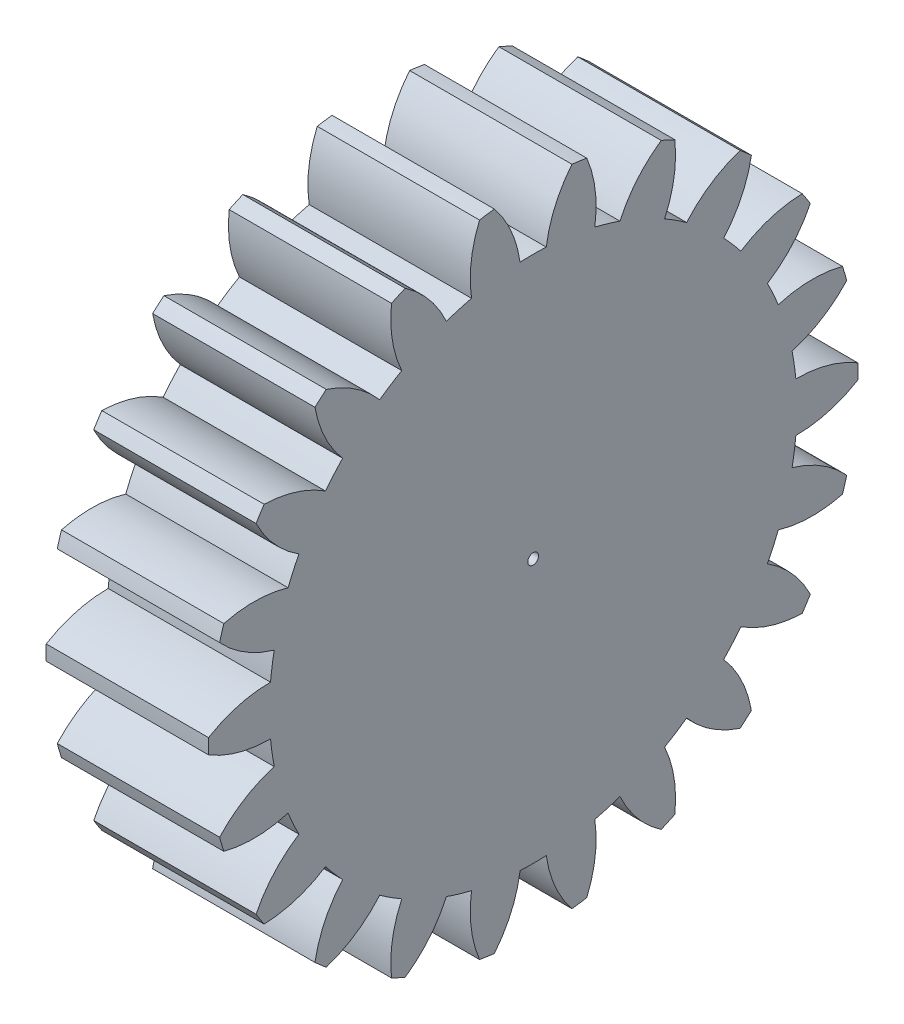
SolidWorks part; units mm, degrees
ref_plane "Plane1" through (0, 0, 0) normal (0, 0, 1) x (1, 0, 0)
ref_plane "Plane2" through (0, 0, 0) normal (0, 1, 0) x (1, 0, 0)
ref_plane "Plane3" through (0, 0, 0) normal (1, 0, 0) x (0, 0, -1)
sketch "HoldingSke" plane through (0, 0, 0) normal (0, 1, 0) x (1, 0, 0)
  line L0 (0, 0) -> (0.4636, -0.1873)
  line L1 (-15, 0) -> (100, 0) construction
  line L2 (0, 0) -> (-2.1039, 2.3779)
  line L3 (0, 0) -> (-11.863, 4.5341)
  line L4 (0, 0) -> (8.0072, 3.2351)
  line L5 (0, 0) -> (-46.8476, -17.4728)
  line L6 (0, 0) -> (-9.9476, -6.7116)
  line L7 (-2.1039, 2.3779) -> (8.6586, 51.2059)
  line L8 (-76.2, 54.61) -> (-76.1, 54.61)
  line L9 (-71.009, 38.7566) -> (-53.1078, 45.2721)
  line L10 (-76.2, 71.12) -> (104.1128, 71.12)
  line L11 (0, 0) -> (-12, 0)
  line L12 (-76.2, 101.6) -> (-76.133, 101.6)
  line L13 (24.9733, 27.94) -> (52.9518, 28.4284)
  line L14 (24.9733, 27.94) -> (24.9743, 27.94)
  line L15 (24.9733, 27.94) -> (100.4006, 29.5858)
  line L16 (-63.627, -2) -> (-12.827, -2)
  circle A0 centre (0, 0) radius 0.4
  circle A1 centre (0, 0) radius 19.499
  circle A2 centre (0, 0) radius 37.5
  circle A3 centre (0, 0) radius 0.4
  dimension "Hub_dia" = 75
  dimension "Bore" = 0.8
  dimension "MBD" = 0.8
  dimension "Overall_len" = 50
  dimension "Thickness" = 12
  dimension "OAL" = 50.0001
  dimension "T_dim" = 0.1
  dimension "Ap" = 20
  dimension "H" = 19.05
  dimension "Pitch_radius" = 180.3128
  dimension "Width" = 12
  dimension "Addendum_fac" = 1
  dimension "Dedendum_fac" = 1.25
  dimension "Clearance_fac" = 0.25
  dimension "Dedendum_add" = 0.001
sketch "BasProSke" plane through (0, 0, 0) normal (0, 1, 0) x (1, 0, 0)
  line L0 (-10, 0) -> (60, 0) construction
  line L1 (0, 0) -> (0, 24)
  line L2 (0, 0) -> (12, 0)
  line L3 (12, 0) -> (12, 24)
  line L4 (12, 24) -> (0, 24)
  dimension "Thickness" = 12
revolve "Base-Revolve" add sketch "BasProSke" angle 360 about L0
sketch "TooCutSke" plane through (0, 0, 0) normal (1, 0, 0) x (0, 0, -1)
  line L1 (0, 0) -> (0, 107) construction
  line L2 (0, 0) -> (-1.6867, 21.9352) construction
  line L3 (0, 0) -> (-6.2482, 43.4572) construction
  line L4 (-1.6867, 21.9352) -> (-3.1241, 21.7286) construction
  arc A0 (0.9682, 19.4749) -> (-0.9682, 19.4749) centre (0, 0) ccw
  arc A1 (2.8856, 23.8515) -> (-2.8856, 23.8515) centre (0, 0) ccw
  circle A2 centre (0, 0) radius 22 construction
  circle A3 centre (0, 0) radius 20.6732 construction
  arc A4 (-0.9682, 19.4749) -> (-2.8856, 23.8515) centre (-9.6845, 18.2645) ccw
  arc A5 (2.8856, 23.8515) -> (0.9682, 19.4749) centre (9.6845, 18.2645) ccw
extrude "ToothCut" cut sketch "TooCutSke" along normal through all
fillet "Breaks" [suppressed] radius 0.04
fillet "RootFillets" [suppressed] radius 0.501
pattern_circular "TeethCuts" count 22 every 16.364 about axis through (-10, 0, 0) along (1, 0, 0) of "ToothCut", "RootFillets", "Breaks"
sketch "HubNeaOneSke" plane through (0, 0, 0) normal (-1, 0, 0) x (0, 0, 1)
  circle A0 centre (0, 0) radius 19.499
extrude "HubNearOne" [suppressed] add sketch "HubNeaOneSke" along normal blind 38.0001
sketch "HubNeaBotSke" plane through (0, 0, 0) normal (-1, 0, 0) x (0, 0, 1)
  circle A0 centre (0, 0) radius 19.499
extrude "HubNearBoth" [suppressed] add sketch "HubNeaBotSke" along normal blind 19
ref_plane "FarPln" through (12, 0, 0) normal (1, 0, 0) x (0, 0, -1)
sketch "HubFarSke" plane through (12, 0, 0) normal (1, 0, 0) x (0, 0, -1)
  circle A0 centre (0, 0) radius 19.499
extrude "HubFar" [suppressed] add sketch "HubFarSke" along normal blind 19
sketch "BorSke" plane through (0, 0, 0) normal (1, 0, 0) x (0, 0, -1)
  circle A0 centre (0, 0) radius 0.4
  dimension "Diameter" = 0.8
extrude "Bore" cut sketch "BorSke" along normal mid plane 100.0001
sketch "KeySke" plane through (0, 0, 0) normal (1, 0, 0) x (0, 0, -1)
  line L0 (-0.05, 0) -> (-0.05, 0.5)
  line L1 (-0.05, 0.5) -> (0.05, 0.5)
  line L2 (0.05, 0.5) -> (0.05, 0)
  line L3 (0, 0) -> (0, 34) construction
  line L4 (-0.05, 0) -> (0.05, 0)
  dimension "Offset" = 0.5
  dimension "Width" = 0.1
extrude "Keyway" [suppressed] cut sketch "KeySke" along normal mid plane 100.0001
pattern_circular "Keyway2" [suppressed] count 2 every 90 about axis through (-10, 0, 0) along (1, 0, 0)
equation "' \"Module@HoldingSke\" = 6.35"
equation "' \"Num_teeth@HoldingSke\" = 12"
equation "' \"Ap@HoldingSke\" =  20"
equation "' \"Ap@HoldingSke\" = 20"
equation "' \"Width@HoldingSke\" = 0.5 * 25.4"
equation "' \"Hub_dia@HoldingSke\"= 1 * 25.4"
equation "' \"Hub_dia@HoldingSke\" = 1 * 25.4"
equation "' \"Overall_len@HoldingSke\" = 1.0 * 25.4"
equation "' \"Bore@HoldingSke\" = 0.75 * 25.4"
equation "' \"T_dim@HoldingSke\" = 0.1 * 25.4"
equation "' \"Width@KeySke\" = 0.25 * 25.4"
equation "' \"Show_teeth@HoldingSke\" = 13"
equation "' \"Backlash@HoldingSke\" = 0.009 * 25.4"
equation "' \"Addendum_fac@HoldingSke\" = 1.0"
equation "' \"Dedendum_fac@HoldingSke\" = 1.25"
equation "' \"Dedendum_add@HoldingSke\" = 0.00005 * 25.4"
equation "' \"Clearance_fac@HoldingSke\" = 0.25"
equation "\"Pitch@HoldingSke\" = 1 / \"Module@HoldingSke\""
equation "\"Overcut_dia@TooCutSke\" = (\"Num_teeth@HoldingSke\" + 2 * \"Addendum_fac@HoldingSke\") / \"Pitch@HoldingSke\" + 0.002 * 25.4"
equation "\"Pitch_dia@TooCutSke\" = \"Num_teeth@HoldingSke\" / \"Pitch@HoldingSke\""
equation "\"Base_dia@TooCutSke\" = \"Num_teeth@HoldingSke\" / \"Pitch@HoldingSke\" * cos((\"Ap@HoldingSke\"  * 3.14159265 / 180))"
equation "\"Root_dia@TooCutSke\" = (\"Num_teeth@HoldingSke\" + 2) / \"Pitch@HoldingSke\" - 2 * (\"Addendum_fac@HoldingSke\" + \"Dedendum_fac@HoldingSke\") / \"Pitch@HoldingSke\" - \"Dedendum_add@HoldingSke\" * 2"
equation "\"Half_ang@TooCutSke\" = 180 / \"Num_teeth@HoldingSke\""
equation "\"Half_CT@TooCutSke\" = \"Num_teeth@HoldingSke\" / \"Pitch@HoldingSke\" * sin((3.14159265 / 2 / \"Num_teeth@HoldingSke\")) / 2 - 7 * \"Backlash@HoldingSke\" / 4"
equation "\"Flank_rad@TooCutSke\" = \"Num_teeth@HoldingSke\" / \"Pitch@HoldingSke\" / 5"
equation "\"Radius@RootFillets\" = \"Clearance_fac@HoldingSke\" / \"Pitch@HoldingSke\" + \"Dedendum_add@HoldingSke\""
equation "\"Break_rad@Breaks\" = 0.02 / \"Pitch@HoldingSke\""
equation "\"Thickness@HoldingSke\" = \"Width@HoldingSke\""
equation "\"OAL@HoldingSke\" = \"Thickness@HoldingSke\""
equation "\"MHD@HoldingSke\" = (\"Num_teeth@HoldingSke\" + 2) / \"Pitch@HoldingSke\" - 2 * (\"Addendum_fac@HoldingSke\" + \"Dedendum_fac@HoldingSke\")  / \"Pitch@HoldingSke\" - \"Dedendum_add@HoldingSke\" * 2"
equation "\"MBD@HoldingSke\" = (\"Num_teeth@HoldingSke\" + 2) / \"Pitch@HoldingSke\" - 2 * (\"Addendum_fac@HoldingSke\" + \"Dedendum_fac@HoldingSke\")  / \"Pitch@HoldingSke\" - \"Dedendum_add@HoldingSke\" * 2 - 0.002 * 25.4"
equation "\"MHD@HoldingSke\" = ((sgn( \"MHD@HoldingSke\" - \"Hub_dia@HoldingSke\" )-1)*( \"MHD@HoldingSke\" - \"Hub_dia@HoldingSke\" ))/-2+ \"Hub_dia@HoldingSke\""
equation "\"MBD@HoldingSke\" = ((sgn( \"MBD@HoldingSke\" - \"Bore@HoldingSke\" )-1)*( \"MBD@HoldingSke\" - \"Bore@HoldingSke\" ))/-2+ \"Bore@HoldingSke\""
equation "\"OAL@HoldingSke\" = ((sgn( \"OAL@HoldingSke\" - \"Overall_len@HoldingSke\" )+1)*( \"OAL@HoldingSke\" - \"Overall_len@HoldingSke\" ))/2 + \"Overall_len@HoldingSke\" + 0.000002 * 25.4"
equation "\"Num_teeth@TeethCuts\" = int( \"Show_teeth@HoldingSke\" ) + 1"
equation "\"Num_teeth@TeethCuts\" = ((sgn( \"Num_teeth@TeethCuts\" - \"Num_teeth@HoldingSke\" )-1)*( \"Num_teeth@TeethCuts\" - \"Num_teeth@HoldingSke\" ))/-2+ \"Num_teeth@HoldingSke\""
equation "\"Num_teeth@TeethCuts\" = ((sgn( \"Num_teeth@TeethCuts\" - 2.0)+1)*( \"Num_teeth@TeethCuts\" - 2.0))/2 +2.0"
equation "\"Angle@TeethCuts\" = 360.0 / \"Num_teeth@HoldingSke\""
equation "\"Diameter@BasProSke\" = (\"Num_teeth@HoldingSke\" + 2 * \"Addendum_fac@HoldingSke\") / \"Pitch@HoldingSke\""
equation "\"Thickness@BasProSke\"  = \"Thickness@HoldingSke\""
equation "' \"Fillet_rad@BasProSke\" =  \"Thickness@HoldingSke\" * 0.05"
equation "' \"Fillet_rad@BasProSke\" = \"Thickness@HoldingSke\" * 0.05"
equation "\"MHD@HoldingSke\" = ((sgn( \"MHD@HoldingSke\" - \"Root_dia@TooCutSke\" )-1)*( \"MHD@HoldingSke\" - \"Root_dia@TooCutSke\" ))/-2+ \"Root_dia@TooCutSke\""
equation "\"Diameter@HubNeaOneSke\" = \"MHD@HoldingSke\""
equation "\"Length@HubNearOne\" = \"OAL@HoldingSke\" - \"Thickness@BasProSke\""
equation "\"Diameter@HubNeaBotSke\" = \"MHD@HoldingSke\""
equation "\"Length@HubNearBoth\" = ( \"OAL@HoldingSke\" - \"Thickness@BasProSke\" ) / 2.0"
equation "\"Thickness@FarPln\" = \"Thickness@BasProSke\""
equation "\"Diameter@HubFarSke\" = \"MHD@HoldingSke\""
equation "\"Length@HubFar\" = ( \"OAL@HoldingSke\" - \"Thickness@BasProSke\" ) / 2.0"
equation "\"Diameter@BorSke\" = \"MBD@HoldingSke\""
equation "\"D1@Bore\" = \"OAL@HoldingSke\" * 2.0"
equation "\"D1@Keyway\" = \"OAL@HoldingSke\" * 2.0"
equation "\"Offset@KeySke\" = \"T_dim@HoldingSke\" + \"MBD@HoldingSke\" / 2.0"
